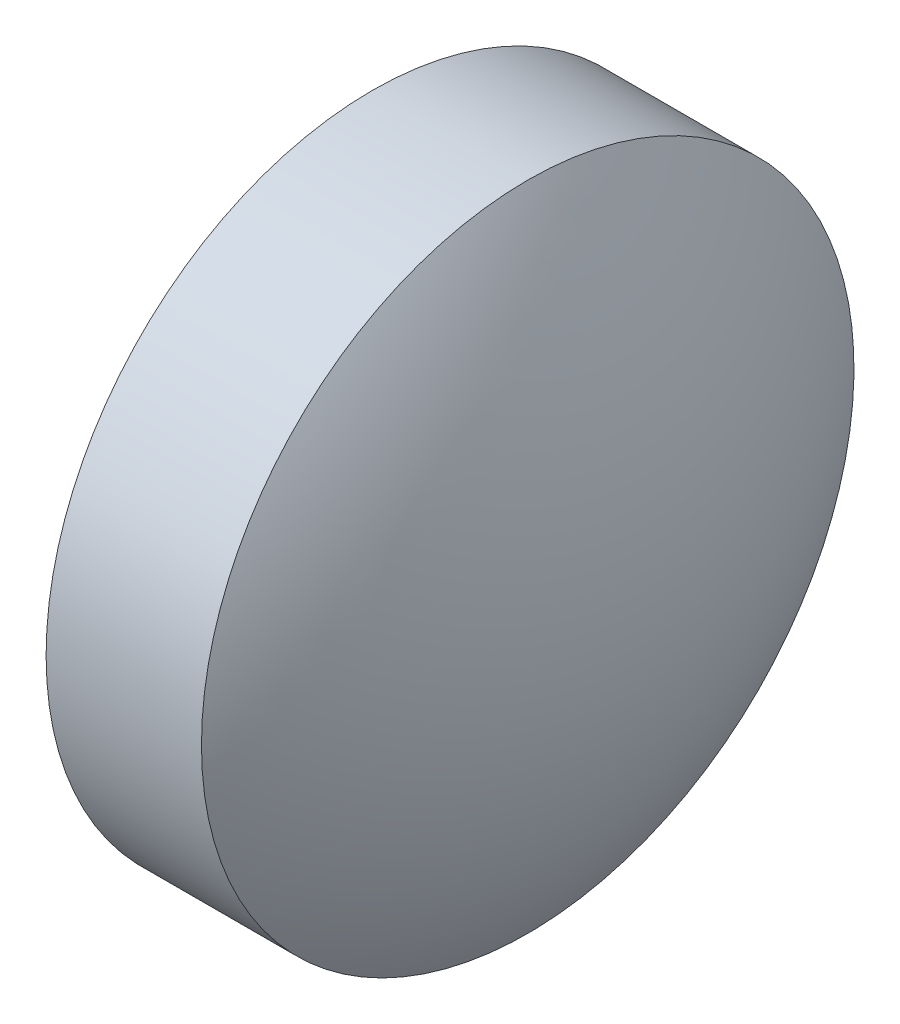
SolidWorks part; units mm, degrees
ref_plane "前视基准面" through (0, 0, 0) normal (0, 0, 1) x (1, 0, 0)
ref_plane "上视基准面" through (0, 0, 0) normal (0, 1, 0) x (1, 0, 0)
ref_plane "右视基准面" through (0, 0, 0) normal (1, 0, 0) x (0, 0, -1)
sketch "草图2" plane through (0, 0, 0) normal (0, 0, 1) x (1, 0, 0)
  line L0 (18.2648, 12.0584) -> (24.7384, 12.0584) construction
  line L1 (20.6944, 15.2084) -> (22.1944, 15.2084)
  line L2 (22.1944, 15.2084) -> (22.1944, 8.9084)
  line L3 (22.1944, 8.9084) -> (20.6944, 8.9084)
  line L4 (20.6944, 8.9084) -> (20.6944, 15.2084)
  arc A0 (20.6944, 15.2084) -> (20.6944, 8.9084) centre (25.6353, 12.0584) ccw
  arc A1 (22.1944, 8.9084) -> (22.1944, 15.2084) centre (17.2536, 12.0584) ccw
  dimension "D1" = 1.5
  dimension "D2" = 6.3
revolve "旋转1" add sketch "草图2" angle 360 about L0
